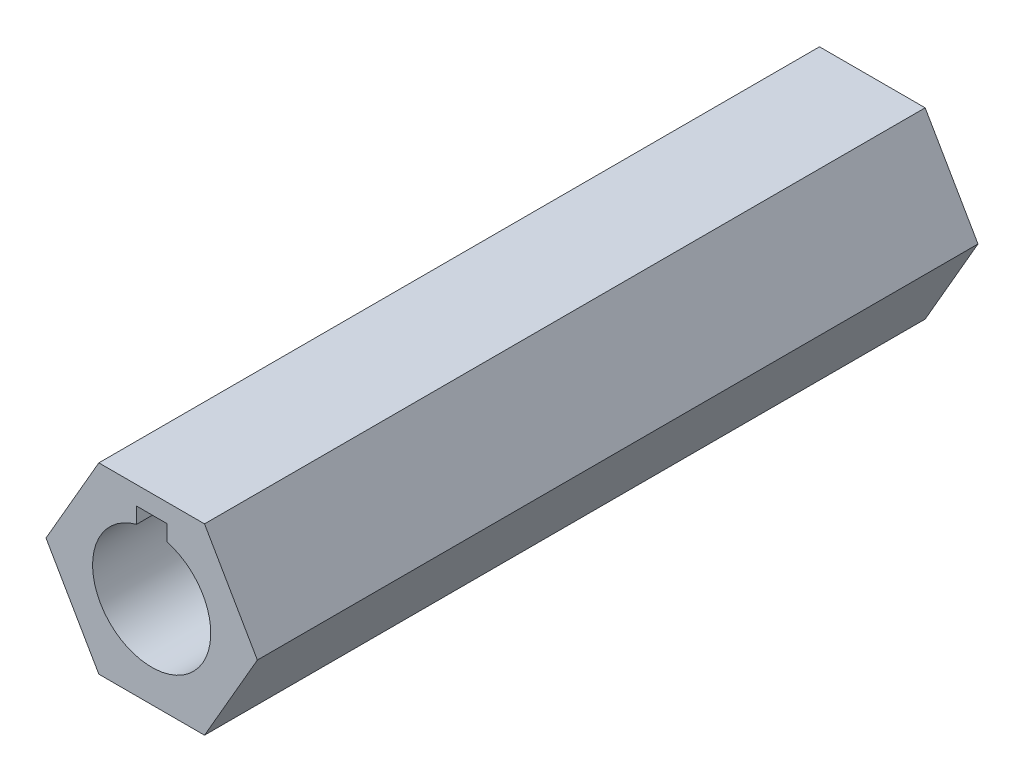
SolidWorks part; units mm, degrees
ref_plane "Front Plane" through (0, 0, 0) normal (0, 0, 1) x (1, 0, 0)
ref_plane "Top Plane" through (0, 0, 0) normal (0, 1, 0) x (1, 0, 0)
ref_plane "Right Plane" through (0, 0, 0) normal (1, 0, 0) x (0, 0, -1)
sketch "Sketch1" plane through (0, 0, 0) normal (0, 0, 1) x (1, 0, 0)
  line L1 (7.3323, 0) -> (3.6662, 6.35)
  line L2 (3.6662, 6.35) -> (-3.6662, 6.35)
  line L3 (-3.6662, 6.35) -> (-7.3323, 0)
  line L4 (-7.3323, 0) -> (-3.6662, -6.35)
  line L5 (-3.6662, -6.35) -> (3.6662, -6.35)
  line L6 (3.6662, -6.35) -> (7.3323, 0)
  circle A0 centre (0, 0) radius 6.35 construction
  dimension "D1" = 12.7
extrude "Boss-Extrude1" add sketch "Sketch1" along normal blind 50
sketch "Sketch2" plane through (0, 0, 50) normal (0, 0, 1) x (1, 0, 0)
  line L0 (-1.0489, 3.9636) -> (-1.0489, 5.063)
  line L1 (-1.0489, 5.063) -> (1.0511, 5.063)
  line L2 (1.0511, 5.063) -> (1.0511, 3.963)
  arc A0 (-1.0489, 3.9636) -> (1.0511, 3.963) centre (0, 0) ccw
  dimension "D1" = 8.2
  dimension "D2" = 2.1
  dimension "D3" = 1.1
extrude "Cut-Extrude1" cut sketch "Sketch2" against normal through all
